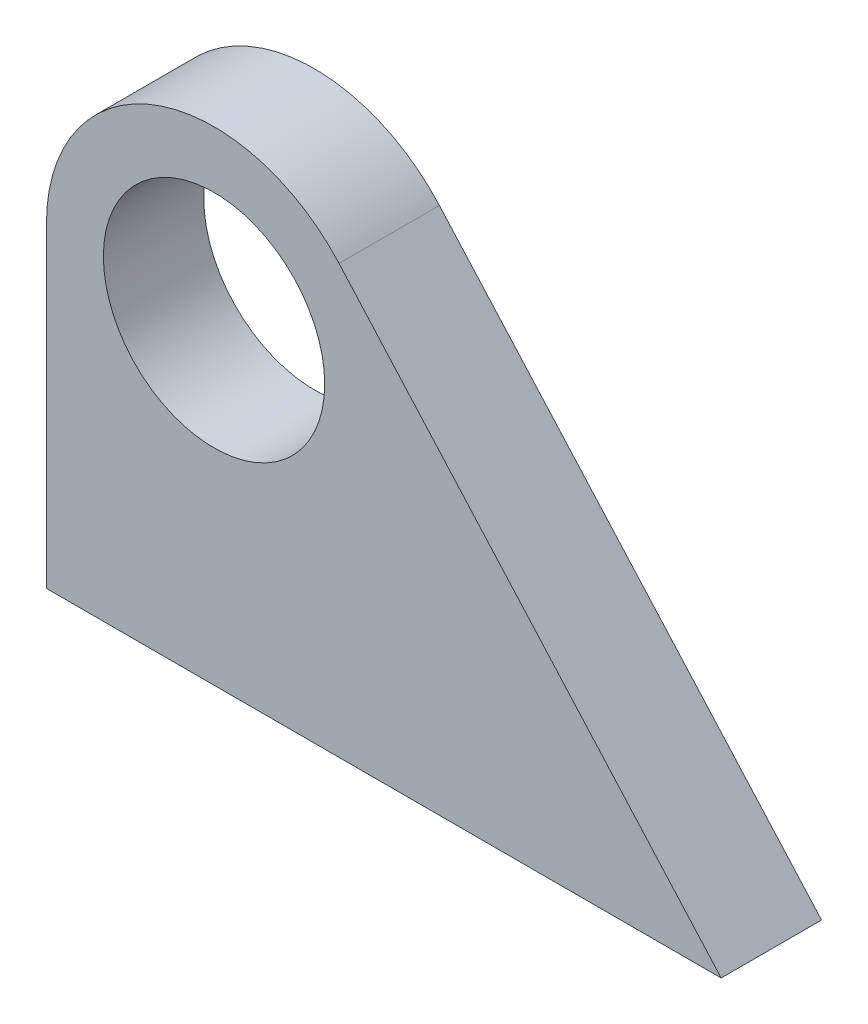
SolidWorks part; units mm, degrees
ref_plane "Alzado" through (0, 0, 0) normal (0, 0, 1) x (1, 0, 0)
ref_plane "Planta" through (0, 0, 0) normal (0, 1, 0) x (1, 0, 0)
ref_plane "Vista lateral" through (0, 0, 0) normal (1, 0, 0) x (0, 0, -1)
sketch "Croquis1" plane through (0, 0, 0) normal (0, 0, 1) x (1, 0, 0)
  line L0 (0, 0) -> (0, 10)
  line L1 (9.2526, 13.5309) -> (21.34, 0)
  line L2 (21.34, 0) -> (0, 0)
  arc A0 (0, 10) -> (9.2526, 13.5309) centre (5.3, 10) cw
  circle A1 centre (5.3, 10) radius 3.5
  dimension "D2" = 1.8
  dimension "D3" = 7
  dimension "D1" = 10
  dimension "D4" = 21.34
extrude "Saliente-Extruir1" add sketch "Croquis1" along normal blind 3.175
